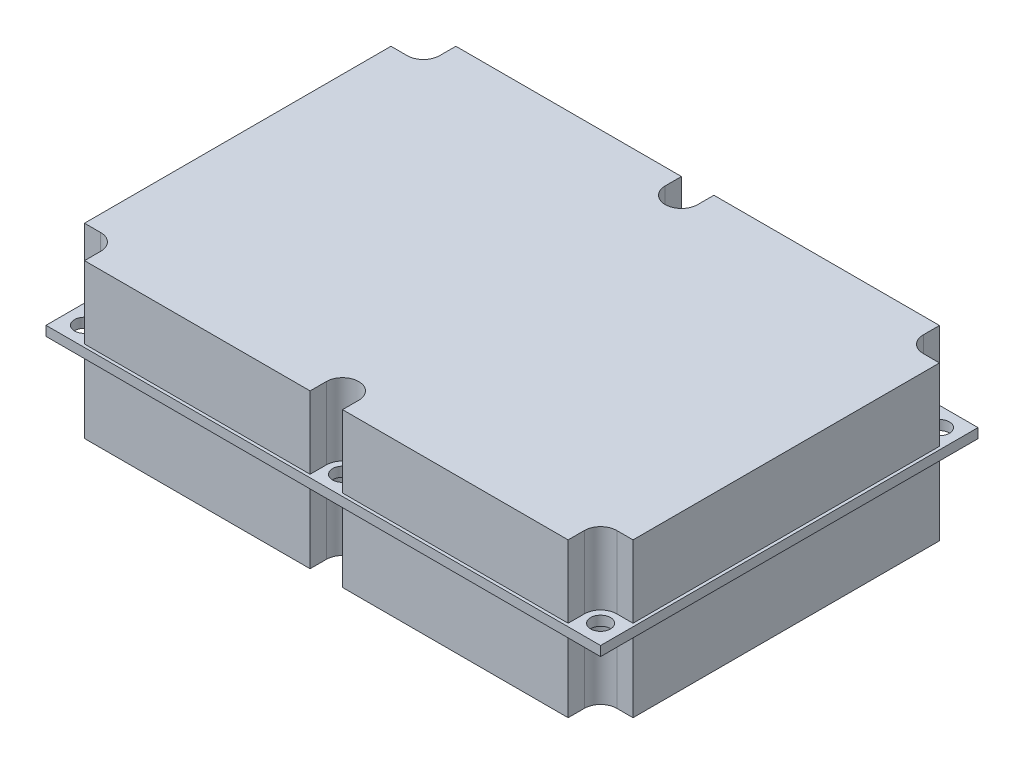
SolidWorks part; units mm, degrees
ref_plane "Front Plane" through (0, 0, 0) normal (0, 0, 1) x (1, 0, 0)
ref_plane "Top Plane" through (0, 0, 0) normal (0, 1, 0) x (1, 0, 0)
ref_plane "Right Plane" through (0, 0, 0) normal (1, 0, 0) x (0, 0, -1)
sketch "Sketch1" plane through (0, 0, 0) normal (0, 1, 0) x (1, 0, 0)
  line L1 (-45.72, 31.115) -> (45.72, 31.115)
  line L2 (-45.72, 31.115) -> (-45.72, -31.115)
  line L3 (-45.72, -31.115) -> (45.72, -31.115)
  line L4 (45.72, 31.115) -> (45.72, -31.115)
  point P4 (0, 31.115)
  point P6 (-45.72, 0)
  dimension "D1" = 62.23
  dimension "D2" = 91.44
extrude "Boss-Extrude1" add sketch "Sketch1" along normal mid plane 1.5875
sketch "Sketch3" plane through (0, 0, 0) normal (0, 1, 0) x (1, 0, 0)
  circle A0 centre (-42.545, 27.94) radius 1.6383
  dimension "D3" = 3.2766
  dimension "D1" = 27.94
  dimension "D2" = 42.545
extrude "Cut-Extrude1" cut sketch "Sketch3" against normal through all and the other way through all
pattern_linear "LPattern1" count 3 spacing 42.545 along (1, 0, 0) count 2 spacing 55.88 along (0, 0, 1) of "Cut-Extrude1"
sketch "Sketch2" plane through (0, 0, 0) normal (0, 1, 0) x (1, 0, 0)
  line L0 (-42.545, 25.265) -> (-45.22, 25.265)
  line L1 (-39.87, 27.94) -> (-39.87, 30.615)
  line L2 (-2.675, 27.94) -> (-2.675, 30.615)
  line L3 (2.675, 27.94) -> (2.675, 30.615)
  line L4 (39.87, 27.94) -> (39.87, 30.615)
  line L5 (42.545, 25.265) -> (45.22, 25.265)
  line L6 (-2.675, 30.615) -> (-39.87, 30.615)
  line L7 (39.87, 30.615) -> (2.675, 30.615)
  line L8 (-45.22, 30.615) -> (-45.22, -30.615)
  line L9 (-45.22, -30.615) -> (45.22, -30.615)
  line L10 (45.22, -30.615) -> (45.22, 30.615)
  line L11 (45.22, 30.615) -> (-45.22, 30.615)
  line L12 (-45.22, 25.265) -> (-45.22, -25.265)
  line L13 (-39.87, -30.615) -> (-2.675, -30.615)
  line L14 (45.22, -25.265) -> (45.22, 25.265)
  line L15 (45.72, 31.115) -> (-45.72, 31.115) construction
  line L16 (-42.545, -25.265) -> (-45.22, -25.265)
  line L17 (-39.87, -27.94) -> (-39.87, -30.615)
  line L18 (-2.675, -27.94) -> (-2.675, -30.615)
  line L19 (2.675, -27.94) -> (2.675, -30.615)
  line L20 (39.87, -27.94) -> (39.87, -30.615)
  line L21 (42.545, -25.265) -> (45.22, -25.265)
  line L22 (2.675, -30.615) -> (39.87, -30.615)
  arc A0 (-42.545, 25.265) -> (-39.87, 27.94) centre (-42.545, 27.94) ccw
  arc A1 (-2.675, 27.94) -> (2.675, 27.94) centre (0, 27.94) ccw
  arc A2 (39.87, 27.94) -> (42.545, 25.265) centre (42.545, 27.94) ccw
  arc A3 (-39.87, -27.94) -> (-42.545, -25.265) centre (-42.545, -27.94) ccw
  arc A4 (2.675, -27.94) -> (-2.675, -27.94) centre (0, -27.94) ccw
  arc A5 (42.545, -25.265) -> (39.87, -27.94) centre (42.545, -27.94) ccw
  dimension "D2" = 0.5
  dimension "D1" = 0.5
extrude "Boss-Extrude2" add sketch "Sketch2" along normal mid plane 25.4 separate body
sketch "Sketch4" plane through (0, 12.7, 0) normal (0, 1, 0) x (1, 0, 0)
  line L0 (-45.22, 0) -> (45.22, 0) construction
  line L1 (-45.22, 25.265) -> (-45.22, -25.265) construction
  line L2 (45.22, -25.265) -> (45.22, 25.265) construction
